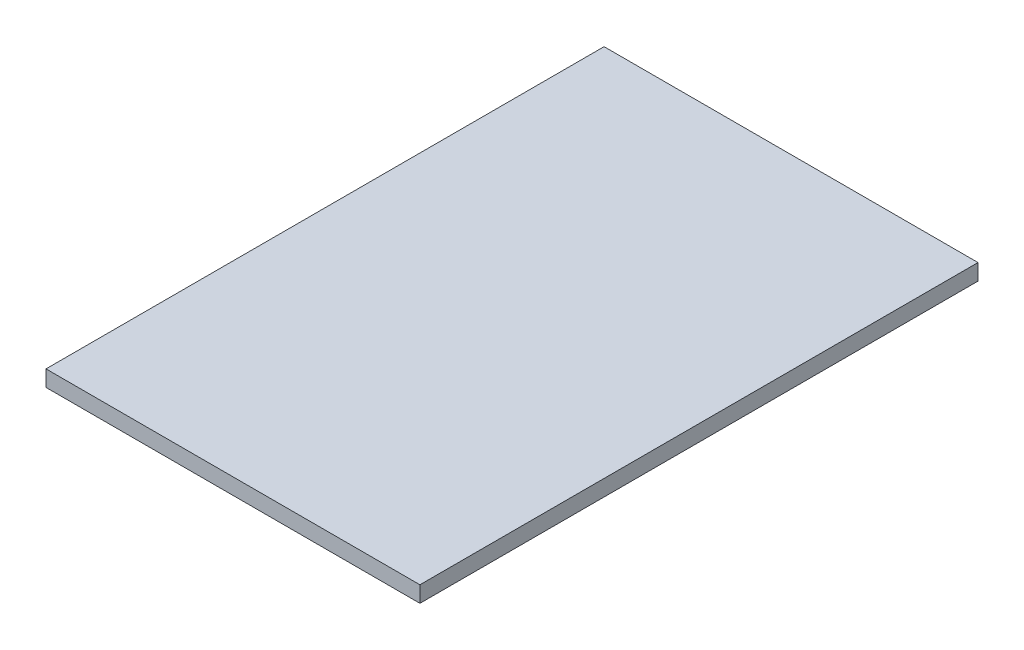
SolidWorks part; units mm, degrees
ref_plane "Front Plane" through (0, 0, 0) normal (0, 0, 1) x (1, 0, 0)
ref_plane "Top Plane" through (0, 0, 0) normal (0, 1, 0) x (1, 0, 0)
ref_plane "Right Plane" through (0, 0, 0) normal (1, 0, 0) x (0, 0, -1)
sketch "Sketch1" plane through (0, 0, 0) normal (0, 0, 1) x (1, 0, 0)
  line L0 (-29.9707, 14.8) -> (-29.9707, -2.8) construction
  line L1 (-70.1707, -2.8) -> (-29.9707, -2.8)
  line L2 (-70.1707, -2.8) -> (-70.1707, -1.0698)
  line L3 (-70.1707, -1.0698) -> (-29.9707, -1.0698)
  line L4 (-29.9707, -2.8) -> (-29.9707, -1.0698)
extrude "Boss-Extrude1" add sketch "Sketch1" along normal blind 60
